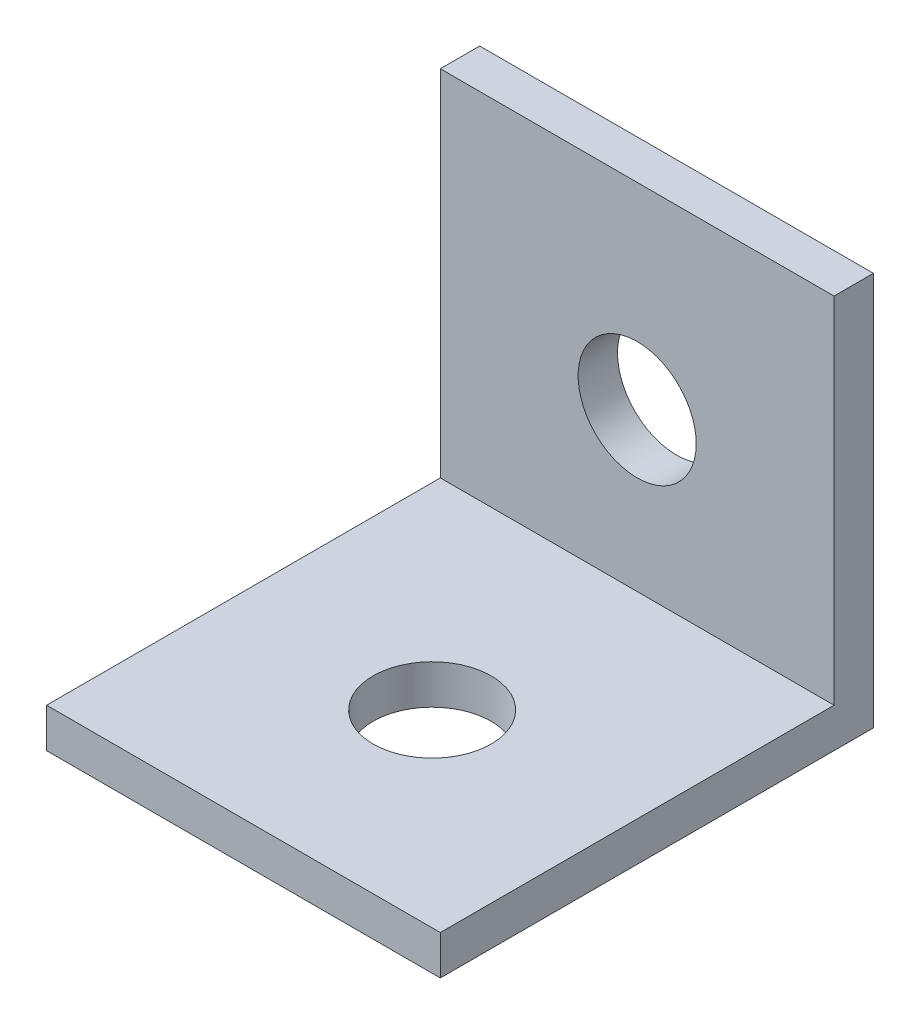
SolidWorks part; units mm, degrees
ref_plane "Front Plane" through (0, 0, 0) normal (0, 0, 1) x (1, 0, 0)
ref_plane "Top Plane" through (0, 0, 0) normal (0, 1, 0) x (1, 0, 0)
ref_plane "Right Plane" through (0, 0, 0) normal (1, 0, 0) x (0, 0, -1)
sketch "Sketch2" plane through (0, 0, 0) normal (0, 0, 1) x (1, 0, 0)
  line L0 (0, 0) -> (20, 0)
  line L1 (20, 0) -> (20, 20)
  line L2 (20, 20) -> (0, 20)
  line L3 (0, 20) -> (0, 0)
  line L4 (0, 0) -> (0.2238, 0.0954)
  dimension "D1" = 20
  dimension "D2" = 20
extrude "Boss-Extrude1" add sketch "Sketch2" along normal blind 2
sketch "Sketch3" plane through (0, 0, 2) normal (0, 0, 1) x (1, 0, 0)
  line L0 (0, 0) -> (0, 2)
  line L1 (0, 20) -> (0, 0) construction
  line L2 (0, 2) -> (20, 2)
  line L3 (20, 0) -> (20, 20) construction
  line L4 (20, 2) -> (20, 0)
  line L5 (20, 0) -> (0, 0)
  dimension "D1" = 2
extrude "Boss-Extrude2" add sketch "Sketch3" along normal blind 20
sketch "Sketch4" plane through (0, 2, 0) normal (0, 1, 0) x (1, 0, 0)
  circle A0 centre (10, -12.4151) radius 3
extrude "Cut-Extrude1" cut sketch "Sketch4" against normal blind 10
sketch "Sketch5" plane through (0, 0, 2) normal (0, 0, 1) x (1, 0, 0)
  line L0 (10, 20) -> (10, 10) construction
  line L1 (20, 20) -> (0, 20) construction
  circle A0 centre (10, 10) radius 3
  dimension "D1" = 10
extrude "Cut-Extrude2" cut sketch "Sketch5" against normal blind 10 contours A0
